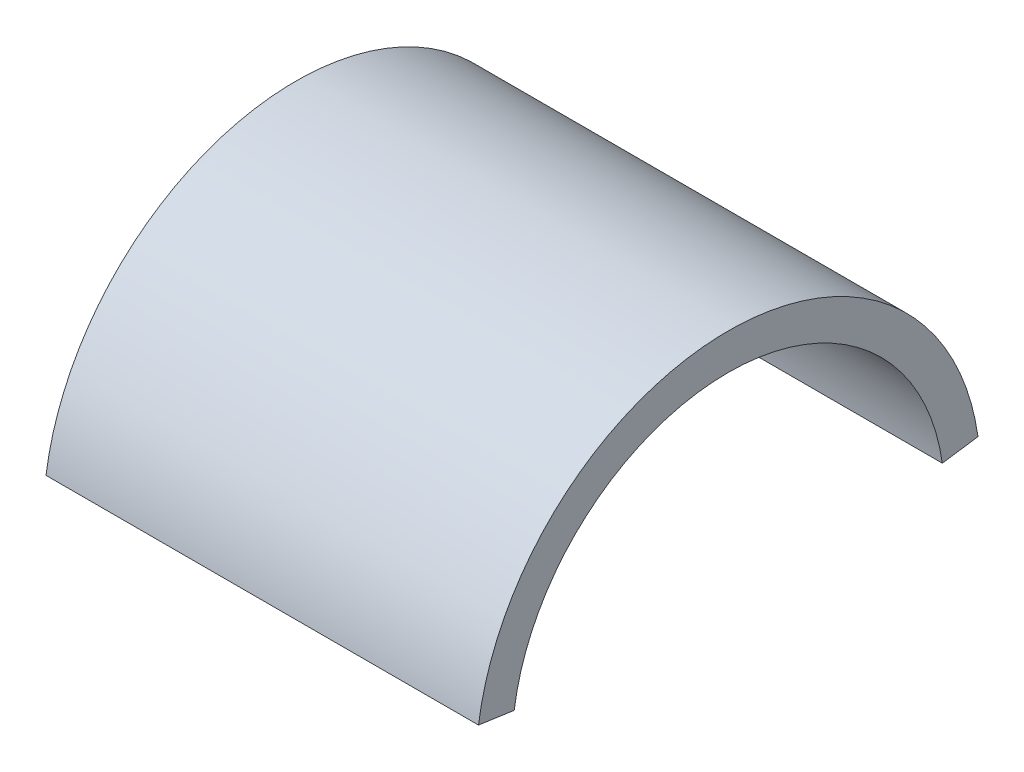
SolidWorks part; units mm, degrees
material "Acrylic (Medium-high impact)"
ref_plane "Front Plane" through (0, 0, 0) normal (0, 0, 1) x (1, 0, 0)
ref_plane "Top Plane" through (0, 0, 0) normal (0, 1, 0) x (1, 0, 0)
ref_plane "Right Plane" through (0, 0, 0) normal (1, 0, 0) x (0, 0, -1)
ref_plane "Plane1" through (53.975, 0, 0) normal (1, 0, 0) x (0, 0, -1)
sketch "Sketch2" plane through (53.975, 0, 0) normal (1, 0, 0) x (0, 0, -1)
  line L0 (-22.0006, 261.9128) -> (-18.8577, 261.4628)
  line L1 (18.8577, 261.4628) -> (22.0006, 261.9128)
  arc A0 (-22.0006, 261.9128) -> (22.0006, 261.9128) centre (0, 258.7625) cw
  arc A1 (-18.8577, 261.4628) -> (18.8577, 261.4628) centre (0, 258.7625) cw
ref_plane "Plane2" through (0, 253.5635, 36.3082) normal (0, 0.9899, 0.1417) x (1, 0, 0)
sketch "Sketch3" plane through (0, 253.5635, 36.3082) normal (0, 0.9899, 0.1417) x (1, 0, 0)
  line L0 (92.075, 58.9035) -> (53.975, 58.9035)
sweep "Sweep1" add profiles "Sketch2" path "Sketch3"
